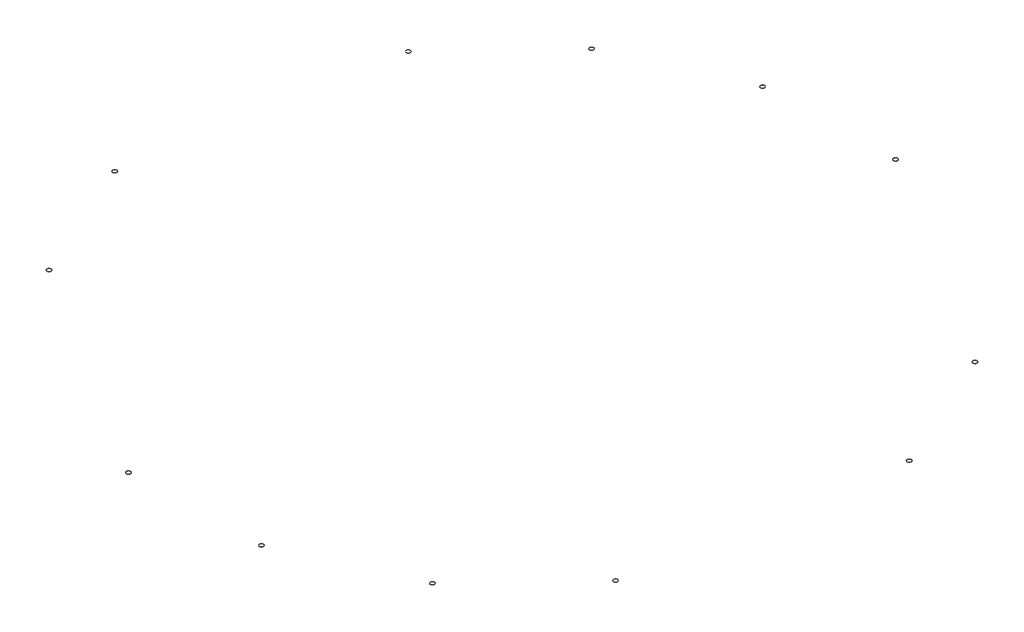
SolidWorks part; units mm, degrees
ref_plane "Front Plane" through (0, 0, 0) normal (0, 0, 1) x (1, 0, 0)
ref_plane "Top Plane" through (0, 0, 0) normal (0, 1, 0) x (1, 0, 0)
ref_plane "Right Plane" through (0, 0, 0) normal (1, 0, 0) x (0, 0, -1)
sketch "Sketch2" plane through (0, 0, 0) normal (0, 1, 0) x (1, 0, 0)
  line L1 (-1580.6599, 3550.2204) -> (1580.6599, -3550.2204) construction
  line L2 (0, 0) -> (0, 3886.2) construction
  line L3 (-2242.9016, 3173.6324) -> (0, 0) construction
  line L4 (0, 0) -> (-3286.6675, 2073.7327) construction
  line L5 (0, 0) -> (-3790.3753, -857.6744) construction
  line L6 (-658.126, -3830.068) -> (0, 0) construction
  line L7 (0, 0) -> (857.6744, -3790.3753) construction
  line L8 (0, 0) -> (-3173.6324, -2242.9016) construction
  line L9 (2242.9016, -3173.6324) -> (0, 0) construction
  line L10 (0, 0) -> (3286.6675, -2073.7327) construction
  line L11 (3790.3753, 857.6744) -> (0, 0) construction
  line L12 (0, 0) -> (3173.6324, 2242.9016) construction
  line L13 (658.126, 3830.068) -> (0, 0) construction
  line L14 (0, 0) -> (-857.6744, 3790.3753) construction
  circle A0 centre (0, 0) radius 3886.2 construction
  circle A1 centre (-2242.9016, 3173.6324) radius 22.225
  circle A2 centre (-3286.6675, 2073.7327) radius 22.225
  circle A3 centre (-3790.3753, -857.6744) radius 22.225
  circle A4 centre (-3173.6324, -2242.9016) radius 22.225
  circle A5 centre (-658.126, -3830.068) radius 22.225
  circle A6 centre (857.6744, -3790.3753) radius 22.225
  circle A7 centre (2242.9016, -3173.6324) radius 22.225
  circle A8 centre (3286.6675, -2073.7327) radius 22.225
  circle A9 centre (-857.6744, 3790.3753) radius 22.225
  circle A10 centre (658.126, 3830.068) radius 22.225
  circle A11 centre (3173.6324, 2242.9016) radius 22.225
  circle A12 centre (3790.3753, 857.6744) radius 22.225
  circle A13 centre (-3790.3753, -857.6744) radius 25.4
  circle A14 centre (-3173.6324, -2242.9016) radius 25.4
  circle A15 centre (-658.126, -3830.068) radius 25.4
  circle A16 centre (857.6744, -3790.3753) radius 25.4
  circle A17 centre (2242.9016, -3173.6324) radius 25.4
  circle A18 centre (3286.6675, -2073.7327) radius 25.4
  circle A19 centre (3790.3753, 857.6744) radius 25.4
  circle A20 centre (3173.6324, 2242.9016) radius 25.4
  circle A21 centre (658.126, 3830.068) radius 25.4
  circle A22 centre (-857.6744, 3790.3753) radius 25.4
  circle A23 centre (-2242.9016, 3173.6324) radius 25.4
  circle A24 centre (-3286.6675, 2073.7327) radius 25.4
  dimension "D2" = 11.25
  dimension "D14" = 7772.4
  dimension "D15" = 44.45
  dimension "D1" = 24
  dimension "D3" = 22.5
  dimension "D4" = 45
  dimension "D5" = 22.5
  dimension "D6" = 11.25
  dimension "D7" = 22.5
  dimension "D8" = 11.25
  dimension "D9" = 22.5
  dimension "D10" = 45
  dimension "D11" = 22.5
  dimension "D12" = 11.25
  dimension "D13" = 22.5
  dimension "D16" = 3.175
  dimension "D17" = 3.175
extrude "Boss-Extrude1" add sketch "Sketch2" along normal blind 3.175
